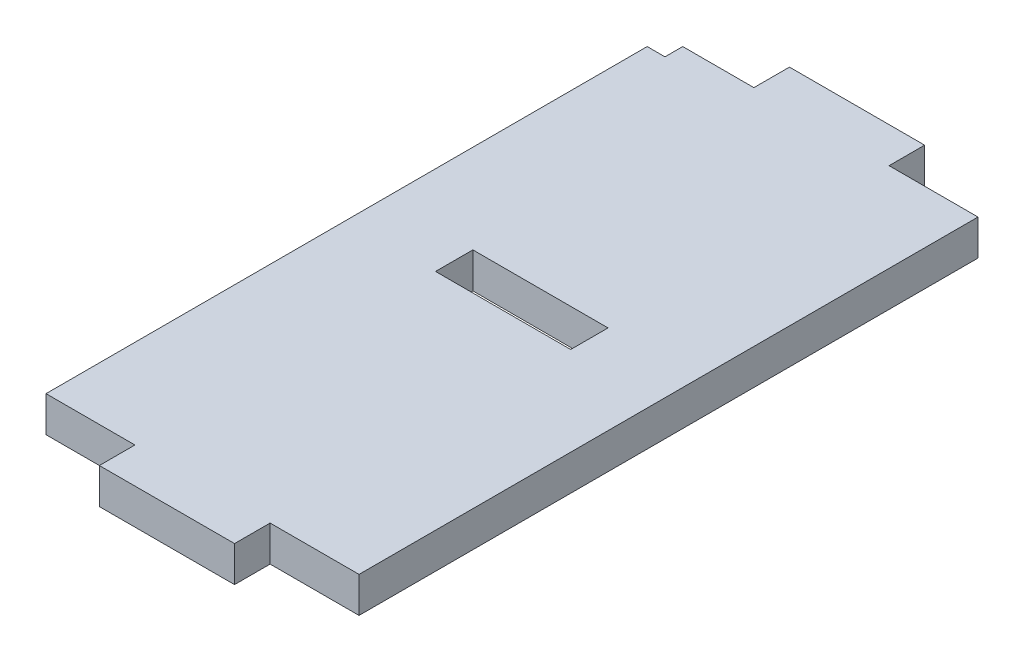
SolidWorks part; units mm, degrees
ref_plane "前视基准面" through (0, 0, 0) normal (0, 0, 1) x (1, 0, 0)
ref_plane "上视基准面" through (0, 0, 0) normal (0, 1, 0) x (1, 0, 0)
ref_plane "右视基准面" through (0, 0, 0) normal (1, 0, 0) x (0, 0, -1)
sketch "草图1" plane through (0, 0, 0) normal (0, 1, 0) x (1, 0, 0)
  line L0 (-2, -2) -> (19.6, -2) construction
  line L1 (0, 0) -> (17.6, 0)
  line L2 (0, 0) -> (0, 34.8)
  line L3 (0, 34.8) -> (17.6, 34.8)
  line L4 (17.6, 0) -> (17.6, 34.8)
  line L5 (19.6, -2) -> (19.6, 36.8) construction
  line L6 (-2, 36.8) -> (19.6, 36.8) construction
  line L7 (-2, -2) -> (-2, 36.8) construction
  line L8 (12.6, 5) -> (12.6, 29.8) construction
  line L9 (5, 29.8) -> (12.6, 29.8) construction
  line L10 (5, 5) -> (5, 29.8) construction
  line L11 (5, 5) -> (12.6, 5) construction
  line L12 (12.6, 5) -> (12.6, -4.6272) construction
  line L13 (5, 5) -> (5, -2) construction
  line L14 (-6.6019, 16.9) -> (28.6178, 16.9) construction
  line L15 (5, 0) -> (12.6, 0)
  line L16 (5, 0) -> (5, -2)
  line L17 (5, -2) -> (12.6, -2)
  line L18 (12.6, 0) -> (12.6, -2)
  line L19 (5, 36.8) -> (12.6, 36.8)
  line L20 (5, 36.8) -> (5, 34.8)
  line L21 (5, 34.8) -> (12.6, 34.8)
  line L22 (12.6, 36.8) -> (12.6, 34.8)
  line L23 (-6.6019, 19) -> (28.6178, 19) construction
  line L24 (-6.6019, 16.9) -> (28.6178, 16.9) construction
  line L25 (5, 19) -> (12.6, 19)
  line L26 (5, 19) -> (5, 16.9)
  line L27 (5, 16.9) -> (12.6, 16.9)
  line L28 (12.6, 19) -> (12.6, 16.9)
  line L30 (0, 34.8) -> (1, 34.8)
  line L31 (0, 34.8) -> (0, 33.8)
  line L32 (0, 33.8) -> (1, 33.8)
  line L33 (1, 34.8) -> (1, 33.8)
  dimension "D1" = 2
  dimension "D2" = 5
  dimension "D3" = 2.1
extrude "凸台-拉伸1" add sketch "草图1" along normal blind 2 contours L1 L4 L3 L2 L25 L28 L27 L26 | L18 L1 L16 L17 | L22 L19 L20 L3
